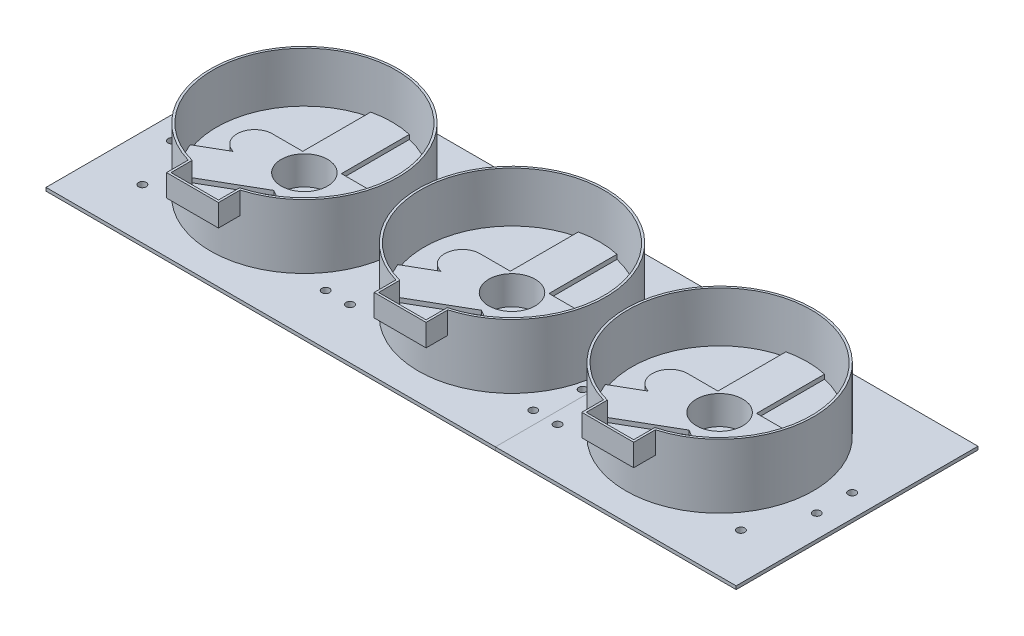
SolidWorks part; units mm, degrees
ref_plane "Front Plane" through (0, 0, 0) normal (0, 0, 1) x (1, 0, 0)
ref_plane "Top Plane" through (0, 0, 0) normal (0, 1, 0) x (1, 0, 0)
ref_plane "Right Plane" through (0, 0, 0) normal (1, 0, 0) x (0, 0, -1)
sketch "Sketch1" plane through (0, 0, 0) normal (0, 1, 0) x (1, 0, 0)
  line L1 (-151.5, 50) -> (151.5, 50)
  line L2 (-151.5, 50) -> (-151.5, -50)
  line L3 (-151.5, -50) -> (151.5, -50)
  line L4 (151.5, 50) -> (151.5, -50)
  line L5 (-151.5, 50) -> (151.5, -50) construction
  line L6 (-151.5, -50) -> (151.5, 50) construction
  point P0 (0, 0)
  dimension "D1" = 100
  dimension "D2" = 303
extrude "Boss-Extrude1" add sketch "Sketch1" along normal blind 3
sketch "Sketch2" plane through (0, 3, 0) normal (0, 1, 0) x (1, 0, 0)
  line L13 (-151.5, -50) -> (151.5, -50) construction
  line L14 (151.5, -50) -> (151.5, 50) construction
  line L15 (-151.5, 50) -> (-151.5, -50) construction
  line L16 (151.5, 50) -> (-151.5, 50) construction
  line L17 (-149.5, 48) -> (-149.5, -48)
  line L18 (-149.5, -48) -> (149.5, -48)
  line L19 (149.5, 48) -> (-149.5, 48)
  line L20 (149.5, -48) -> (149.5, 48)
  line L21 (-149.5, 48) -> (-149.5, -48)
  line L22 (-149.5, -48) -> (149.5, -48)
  line L23 (149.5, 48) -> (-149.5, 48)
  line L24 (149.5, -48) -> (149.5, 48)
  line L25 (-151.5, -50) -> (151.5, -50)
  line L26 (151.5, -50) -> (151.5, 50)
  line L27 (-151.5, 50) -> (-151.5, -50)
  line L28 (151.5, 50) -> (-151.5, 50)
  line M9 (151.5, -50) -> (151.5, 50)
  line M10 (151.5, 50) -> (-151.5, 50)
  line M11 (-151.5, 50) -> (-151.5, -50)
  line M12 (-151.5, -50) -> (151.5, -50)
  dimension "D1" = 2
extrude "Boss-Extrude3" add sketch "Sketch2" along normal blind 1.5 contours L24 L22 L21 L23 M12 M9 M10 M11
sketch "Sketch3" plane through (151.5, 0, 0) normal (1, 0, 0) x (0, 0, -1)
  line L0 (50, 4.5) -> (50, 0) construction
  line L1 (-50, 4.5) -> (50, 4.5)
  line L2 (-50, 4.5) -> (-50, 3)
  line L3 (-50, 3) -> (50, 3)
  line L4 (50, 4.5) -> (50, 3)
  dimension "D1" = 1.5
extrude "Boss-Extrude4" add sketch "Sketch3" along normal blind 4.75
sketch "Sketch5" plane through (0, 3, 0) normal (0, 1, 0) x (1, 0, 0)
  line L0 (149.5, -48) -> (149.5, 48) construction
  line L1 (0, 0) -> (0, 65.2785) construction
  line L2 (26.8157, -29.3425) -> (0, -13.8605)
  line L3 (-8.75, 38.775) -> (-8.75, 1.295)
  line L4 (8.75, 38.775) -> (8.75, 1.295)
  line L5 (36.8421, -14.924) -> (8.75, 1.295)
  line L6 (-36.8421, -14.924) -> (-8.75, 1.295)
  line L7 (-26.8157, -29.3425) -> (0, -13.8605)
  line L9 (-47, 60.0397) -> (-47, -70.5831) construction
  line L10 (5.6339, -7.0096) -> (33.9368, -23.3502) construction
  line L11 (-6.1109, -7.285) -> (-42.2034, -28.1229) construction
  line L12 (102.75, 38.775) -> (102.75, 1.295)
  line L13 (85.25, 38.775) -> (85.25, 1.295)
  line L14 (57.1579, -14.924) -> (85.25, 1.295)
  line L15 (67.1843, -29.3425) -> (94, -13.8605)
  line L16 (47, 76.7498) -> (47, -70.5831) construction
  line L17 (120.8157, -29.3425) -> (94, -13.8605)
  line L18 (130.8421, -14.924) -> (102.75, 1.295)
  line L19 (-67.1843, -29.3425) -> (-94, -13.8605)
  line L20 (-120.8157, -29.3425) -> (-94, -13.8605)
  line L21 (-130.8421, -14.924) -> (-102.75, 1.295)
  line L22 (-102.75, 38.775) -> (-102.75, 1.295)
  line L23 (-85.25, 38.775) -> (-85.25, 1.295)
  line L24 (-57.1579, -14.924) -> (-85.25, 1.295)
  circle A3 centre (0, 0) radius 39.75
  arc A6 (26.8157, -29.3425) -> (-26.8157, -29.3425) centre (0, 0) cw
  arc A7 (36.8421, -14.924) -> (8.75, 38.775) centre (0, 0) ccw
  arc A8 (-8.75, 38.775) -> (-36.8421, -14.924) centre (0, 0) ccw
  circle A9 centre (94, 0) radius 39.75
  circle A10 centre (-94, 0) radius 39.75
  dimension "D1" = 79.5
  dimension "D2" = 37.48
  dimension "D3" = 17.5
  dimension "D4" = 17.5
  dimension "D9" = 14.5
  dimension "D10" = 14.5
  dimension "D5" = 17.5
  dimension "D6" = 120
  dimension "D7" = 8.75
  dimension "D8" = 8.75
extrude "Cut-Extrude2" cut sketch "Sketch5" against normal blind 2 contours A10 L23 L24 | A10 L21 L22 | A10 L19 L20 | L3 A3 L6 | L7 A3 L2 | L5 A3 L4 | A9 L12 L18 | A9 L17 L15 | A9 L14 L13
sketch "Sketch6" plane through (0, 1, 0) normal (0, 1, 0) x (1, 0, 0)
  line L1 (-6.5, -26.3605) -> (6.5, -26.3605)
  line L2 (-8.5, -28.3605) -> (-8.5, -35.3605)
  line L3 (-6.5, -37.3605) -> (6.5, -37.3605)
  line L4 (8.5, -28.3605) -> (8.5, -35.3605)
  line L5 (-8.5, -26.3605) -> (8.5, -37.3605) construction
  line L6 (-8.5, -37.3605) -> (8.5, -26.3605) construction
  line L7 (-100.5, -26.3605) -> (-87.5, -26.3605)
  line L8 (-102.5, -28.3605) -> (-102.5, -35.3605)
  line L9 (-100.5, -37.3605) -> (-87.5, -37.3605)
  line L10 (-85.5, -28.3605) -> (-85.5, -35.3605)
  line L11 (-102.5, -26.3605) -> (-85.5, -37.3605) construction
  line L12 (-102.5, -37.3605) -> (-85.5, -26.3605) construction
  line L13 (87.5, -26.3605) -> (100.5, -26.3605)
  line L14 (85.5, -28.3605) -> (85.5, -35.3605)
  line L15 (87.5, -37.3605) -> (100.5, -37.3605)
  line L16 (102.5, -28.3605) -> (102.5, -35.3605)
  line L17 (85.5, -26.3605) -> (102.5, -37.3605) construction
  line L18 (85.5, -37.3605) -> (102.5, -26.3605) construction
  arc A0 (-6.5, -26.3605) -> (-8.5, -28.3605) centre (-6.5, -28.3605) ccw
  arc A1 (-8.5, -35.3605) -> (-6.5, -37.3605) centre (-6.5, -35.3605) ccw
  arc A2 (6.5, -37.3605) -> (8.5, -35.3605) centre (6.5, -35.3605) ccw
  arc A3 (6.5, -26.3605) -> (8.5, -28.3605) centre (6.5, -28.3605) cw
  arc A5 (-87.5, -37.3605) -> (-85.5, -35.3605) centre (-87.5, -35.3605) ccw
  arc A6 (-102.5, -35.3605) -> (-100.5, -37.3605) centre (-100.5, -35.3605) ccw
  arc A7 (-100.5, -26.3605) -> (-102.5, -28.3605) centre (-100.5, -28.3605) ccw
  arc A8 (-87.5, -26.3605) -> (-85.5, -28.3605) centre (-87.5, -28.3605) cw
  arc A9 (85.5, -35.3605) -> (87.5, -37.3605) centre (87.5, -35.3605) ccw
  arc A10 (100.5, -37.3605) -> (102.5, -35.3605) centre (100.5, -35.3605) ccw
  arc A11 (100.5, -26.3605) -> (102.5, -28.3605) centre (100.5, -28.3605) cw
  arc A12 (87.5, -26.3605) -> (85.5, -28.3605) centre (87.5, -28.3605) ccw
  point P0 (0, -31.8605)
  point P5 (-94, -31.8605)
  point P39 (94, -31.8605)
  dimension "D4" = 2
  dimension "D5" = 12.5
  dimension "D8" = 2
  dimension "D12" = 2
  dimension "D1" = 12.5
  dimension "D2" = 11
  dimension "D3" = 17
  dimension "D6" = 17
  dimension "D7" = 11
  dimension "D9" = 12.5
  dimension "D10" = 11
  dimension "D11" = 17
extrude "Cut-Extrude3" cut sketch "Sketch6" against normal through all both and the other way through all
mirror "Mirror1" about plane through (0, 0, 0) normal (1, 0, 0) of "Boss-Extrude4"
sketch "Sketch7" plane through (0, 0, 50) normal (0, 0, 1) x (1, 0, 0)
  line L1 (156.25, 4.5) -> (-156.25, 4.5)
  line L2 (156.25, 4.5) -> (156.25, 3)
  line L3 (156.25, 3) -> (-156.25, 3)
  line L4 (-156.25, 4.5) -> (-156.25, 3)
extrude "Boss-Extrude5" add sketch "Sketch7" along normal blind 4.75
mirror "Mirror2" about plane through (0, 0, 0) normal (0, 0, 1) of "Boss-Extrude5"
sketch "Sketch8" plane through (0, 3, 0) normal (0, 1, 0) x (1, 0, 0)
  line L0 (-22.5, 0) -> (22.5, 0) construction
  line L1 (-22.5, 8) -> (22.5, 8)
  line L2 (-22.5, -8) -> (22.5, -8)
  line L3 (47, 67.8149) -> (47, -81.6541) construction
  line L4 (-47, 71.8097) -> (-47, -81.6541) construction
  line L5 (116.5, 0) -> (71.5, 0) construction
  line L6 (116.5, 8) -> (71.5, 8)
  line L7 (116.5, -8) -> (71.5, -8)
  line L8 (-71.5, 0) -> (-116.5, 0) construction
  line L9 (-71.5, 8) -> (-116.5, 8)
  line L10 (-71.5, -8) -> (-116.5, -8)
  arc A0 (-22.5, 8) -> (-22.5, -8) centre (-22.5, 0) ccw
  arc A1 (22.5, -8) -> (22.5, 8) centre (22.5, 0) ccw
  arc A13 (116.5, 8) -> (116.5, -8) centre (116.5, 0) cw
  arc A14 (71.5, -8) -> (71.5, 8) centre (71.5, 0) cw
  arc A15 (-71.5, 8) -> (-71.5, -8) centre (-71.5, 0) cw
  arc A16 (-116.5, -8) -> (-116.5, 8) centre (-116.5, 0) cw
  point P2 (0, 0)
  point P15 (-94, 0)
  point P27 (94, 0)
  dimension "D2" = 8
  dimension "D1" = 45
  dimension "D3" = 94
  dimension "D4" = 47
extrude "Boss-Extrude6" add sketch "Sketch8" against normal up to surface (2 mm away) up to face at (-116.2558, 1, -10.5488)
sketch "Sketch9" plane through (0, 3, 0) normal (0, 1, 0) x (1, 0, 0)
  line L0 (-94, 61.6552) -> (-94, -65.6755) construction
  line L1 (94, 61.6552) -> (94, -59.8308) construction
  circle A0 centre (0, 0) radius 10.5
  circle A3 centre (94, 0) radius 10.5
  circle A4 centre (-94, 0) radius 10.5
  dimension "D1" = 21
  dimension "D2" = 21
  dimension "D3" = 21
  dimension "D4" = 94
  dimension "D5" = 94
extrude "Cut-Extrude4" cut sketch "Sketch9" against normal up to surface (2 mm away) up to face at (-118.1353, 1, -7.8892)
sketch "Sketch11" plane through (0, 1, 0) normal (0, 1, 0) x (1, 0, 0)
  circle A0 centre (0, 0) radius 6
  circle A1 centre (94, 0) radius 6
  circle A2 centre (-94, 0) radius 6
  circle A3 centre (94, 0) radius 10.5 construction
  dimension "D1" = 12
  dimension "D2" = 12
  dimension "D3" = 12
extrude "Cut-Extrude5" cut sketch "Sketch11" against normal through all both and the other way through all
sketch "Sketch12" plane through (0, 3, 0) normal (0, 1, 0) x (1, 0, 0)
  line L0 (116.5, 8) -> (102.75, 8) construction
  line L1 (130.8421, -14.924) -> (118.4371, -7.7619) construction
  line L2 (102.75, 38.775) -> (102.75, 8) construction
  line L3 (67.1843, -29.3425) -> (94, -13.8605) construction
  line L4 (120.8157, -29.3425) -> (94, -13.8605) construction
  line L5 (85.25, 38.775) -> (85.25, 8) construction
  line L6 (85.25, 8) -> (71.5, 8) construction
  line L7 (57.1579, -14.924) -> (69.5629, -7.7619) construction
  line L8 (36.8421, -14.924) -> (24.4371, -7.7619) construction
  line L9 (22.5, 8) -> (8.75, 8) construction
  line L10 (8.75, 38.775) -> (8.75, 8) construction
  line L11 (-26.8157, -29.3425) -> (0, -13.8605) construction
  line L12 (26.8157, -29.3425) -> (0, -13.8605) construction
  line L13 (-36.8421, -14.924) -> (-24.4371, -7.7619) construction
  line L14 (-8.75, 8) -> (-22.5, 8) construction
  line L15 (-8.75, 38.775) -> (-8.75, 8) construction
  line L16 (-57.1579, -14.924) -> (-69.5629, -7.7619) construction
  line L17 (-71.5, 8) -> (-85.25, 8) construction
  line L18 (-85.25, 38.775) -> (-85.25, 8) construction
  line L19 (-120.8157, -29.3425) -> (-94, -13.8605) construction
  line L20 (-67.1843, -29.3425) -> (-94, -13.8605) construction
  line L21 (-130.8421, -14.924) -> (-118.4371, -7.7619) construction
  line L22 (-102.75, 8) -> (-116.5, 8) construction
  line L23 (-102.75, 38.775) -> (-102.75, 8) construction
  line L24 (-149.5, 48) -> (-149.5, -48) construction
  line L25 (-149.5, -48) -> (149.5, -48) construction
  line L26 (149.5, -48) -> (149.5, 48) construction
  line L27 (149.5, 48) -> (-149.5, 48) construction
  line L28 (116.5, 8) -> (102.75, 8)
  line L29 (130.8421, -14.924) -> (118.4371, -7.7619)
  line L30 (102.75, 38.775) -> (102.75, 8)
  line L31 (67.1843, -29.3425) -> (94, -13.8605)
  line L32 (120.8157, -29.3425) -> (94, -13.8605)
  line L33 (85.25, 38.775) -> (85.25, 8)
  line L34 (85.25, 8) -> (71.5, 8)
  line L35 (57.1579, -14.924) -> (69.5629, -7.7619)
  line L36 (36.8421, -14.924) -> (24.4371, -7.7619)
  line L37 (22.5, 8) -> (8.75, 8)
  line L38 (8.75, 38.775) -> (8.75, 8)
  line L39 (-26.8157, -29.3425) -> (0, -13.8605)
  line L40 (26.8157, -29.3425) -> (0, -13.8605)
  line L41 (-36.8421, -14.924) -> (-24.4371, -7.7619)
  line L42 (-8.75, 8) -> (-22.5, 8)
  line L43 (-8.75, 38.775) -> (-8.75, 8)
  line L44 (-57.1579, -14.924) -> (-69.5629, -7.7619)
  line L45 (-71.5, 8) -> (-85.25, 8)
  line L46 (-85.25, 38.775) -> (-85.25, 8)
  line L47 (-120.8157, -29.3425) -> (-94, -13.8605)
  line L48 (-67.1843, -29.3425) -> (-94, -13.8605)
  line L49 (-130.8421, -14.924) -> (-118.4371, -7.7619)
  line L50 (-102.75, 8) -> (-116.5, 8)
  line L51 (-102.75, 38.775) -> (-102.75, 8)
  line L52 (-149.5, 48) -> (-149.5, -48)
  line L53 (-149.5, -48) -> (149.5, -48)
  line L54 (149.5, -48) -> (149.5, 48)
  line L55 (149.5, 48) -> (-149.5, 48)
  arc A0 (118.4371, -7.7619) -> (116.5, 8) centre (116.5, 0) ccw construction
  arc A1 (130.8421, -14.924) -> (102.75, 38.775) centre (94, 0) ccw construction
  arc A2 (67.1843, -29.3425) -> (120.8157, -29.3425) centre (94, 0) ccw construction
  circle A3 centre (94, 0) radius 10.5 construction
  arc A4 (71.5, 8) -> (69.5629, -7.7619) centre (71.5, 0) ccw construction
  arc A5 (85.25, 38.775) -> (57.1579, -14.924) centre (94, 0) ccw construction
  arc A6 (24.4371, -7.7619) -> (22.5, 8) centre (22.5, 0) ccw construction
  arc A7 (36.8421, -14.924) -> (8.75, 38.775) centre (0, 0) ccw construction
  arc A8 (-26.8157, -29.3425) -> (26.8157, -29.3425) centre (0, 0) ccw construction
  circle A9 centre (0, 0) radius 10.5 construction
  arc A10 (-22.5, 8) -> (-24.4371, -7.7619) centre (-22.5, 0) ccw construction
  arc A11 (-8.75, 38.775) -> (-36.8421, -14.924) centre (0, 0) ccw construction
  circle A12 centre (-94, 0) radius 10.5 construction
  arc A13 (-69.5629, -7.7619) -> (-71.5, 8) centre (-71.5, 0) ccw construction
  arc A14 (-57.1579, -14.924) -> (-85.25, 38.775) centre (-94, 0) ccw construction
  arc A15 (-120.8157, -29.3425) -> (-67.1843, -29.3425) centre (-94, 0) ccw construction
  arc A16 (-116.5, 8) -> (-118.4371, -7.7619) centre (-116.5, 0) ccw construction
  arc A17 (-102.75, 38.775) -> (-130.8421, -14.924) centre (-94, 0) ccw construction
  arc A18 (118.4371, -7.7619) -> (116.5, 8) centre (116.5, 0) ccw
  arc A19 (130.8421, -14.924) -> (102.75, 38.775) centre (94, 0) ccw
  arc A20 (67.1843, -29.3425) -> (120.8157, -29.3425) centre (94, 0) ccw
  circle A21 centre (94, 0) radius 10.5
  arc A22 (71.5, 8) -> (69.5629, -7.7619) centre (71.5, 0) ccw
  arc A23 (85.25, 38.775) -> (57.1579, -14.924) centre (94, 0) ccw
  arc A24 (24.4371, -7.7619) -> (22.5, 8) centre (22.5, 0) ccw
  arc A25 (36.8421, -14.924) -> (8.75, 38.775) centre (0, 0) ccw
  arc A26 (-26.8157, -29.3425) -> (26.8157, -29.3425) centre (0, 0) ccw
  circle A27 centre (0, 0) radius 10.5
  arc A28 (-22.5, 8) -> (-24.4371, -7.7619) centre (-22.5, 0) ccw
  arc A29 (-8.75, 38.775) -> (-36.8421, -14.924) centre (0, 0) ccw
  circle A30 centre (-94, 0) radius 10.5
  arc A31 (-69.5629, -7.7619) -> (-71.5, 8) centre (-71.5, 0) ccw
  arc A32 (-57.1579, -14.924) -> (-85.25, 38.775) centre (-94, 0) ccw
  arc A33 (-120.8157, -29.3425) -> (-67.1843, -29.3425) centre (-94, 0) ccw
  arc A34 (-116.5, 8) -> (-118.4371, -7.7619) centre (-116.5, 0) ccw
  arc A35 (-102.75, 38.775) -> (-130.8421, -14.924) centre (-94, 0) ccw
extrude "Boss-Extrude8" add sketch "Sketch12" along normal blind 11
sketch "Sketch13" plane through (0, 1, 0) normal (0, 1, 0) x (1, 0, 0)
  line L0 (87.5, -37.3605) -> (100.5, -37.3605) construction
  line L1 (102.5, -35.3605) -> (102.5, -28.3605) construction
  line L2 (85.5, -28.3605) -> (85.5, -35.3605) construction
  line L3 (100.5, -26.3605) -> (87.5, -26.3605) construction
  line L4 (-85.5, -35.3605) -> (-85.5, -28.3605) construction
  line L5 (-100.5, -37.3605) -> (-87.5, -37.3605) construction
  line L6 (-102.5, -28.3605) -> (-102.5, -35.3605) construction
  line L7 (-87.5, -26.3605) -> (-100.5, -26.3605) construction
  line L8 (-6.5, -37.3605) -> (6.5, -37.3605) construction
  line L9 (8.5, -35.3605) -> (8.5, -28.3605) construction
  line L10 (6.5, -26.3605) -> (-6.5, -26.3605) construction
  line L11 (-8.5, -28.3605) -> (-8.5, -35.3605) construction
  line L12 (87.5, -37.3605) -> (100.5, -37.3605)
  line L13 (102.5, -35.3605) -> (102.5, -28.3605)
  line L14 (85.5, -28.3605) -> (85.5, -35.3605)
  line L15 (100.5, -26.3605) -> (87.5, -26.3605)
  line L16 (-85.5, -35.3605) -> (-85.5, -28.3605)
  line L17 (-100.5, -37.3605) -> (-87.5, -37.3605)
  line L18 (-102.5, -28.3605) -> (-102.5, -35.3605)
  line L19 (-87.5, -26.3605) -> (-100.5, -26.3605)
  line L20 (-6.5, -37.3605) -> (6.5, -37.3605)
  line L21 (8.5, -35.3605) -> (8.5, -28.3605)
  line L22 (6.5, -26.3605) -> (-6.5, -26.3605)
  line L23 (-8.5, -28.3605) -> (-8.5, -35.3605)
  line L24 (120.8157, -29.3425) -> (94, -13.8605) construction
  line L25 (67.1843, -29.3425) -> (94, -13.8605) construction
  line L26 (26.8157, -29.3425) -> (0, -13.8605) construction
  line L27 (-26.8157, -29.3425) -> (0, -13.8605) construction
  line L28 (-120.8157, -29.3425) -> (-94, -13.8605) construction
  line L29 (-67.1843, -29.3425) -> (-94, -13.8605) construction
  line L30 (120.8157, -29.3425) -> (94, -13.8605)
  line L31 (67.1843, -29.3425) -> (94, -13.8605)
  line L32 (26.8157, -29.3425) -> (0, -13.8605)
  line L33 (-26.8157, -29.3425) -> (0, -13.8605)
  line L34 (-120.8157, -29.3425) -> (-94, -13.8605)
  line L35 (-67.1843, -29.3425) -> (-94, -13.8605)
  line L36 (118.4371, -7.7619) -> (130.8421, -14.924) construction
  line L37 (102.75, 38.775) -> (102.75, 8) construction
  line L38 (102.75, 8) -> (116.5, 8) construction
  line L39 (71.5, 8) -> (85.25, 8) construction
  line L40 (85.25, 8) -> (85.25, 38.775) construction
  line L41 (57.1579, -14.924) -> (69.5629, -7.7619) construction
  line L42 (8.75, 8) -> (22.5, 8) construction
  line L43 (24.4371, -7.7619) -> (36.8421, -14.924) construction
  line L44 (8.75, 38.775) -> (8.75, 8) construction
  line L45 (-22.5, 8) -> (-8.75, 8) construction
  line L46 (-8.75, 8) -> (-8.75, 38.775) construction
  line L47 (-36.8421, -14.924) -> (-24.4371, -7.7619) construction
  line L48 (-116.5, 8) -> (-102.75, 8) construction
  line L49 (-102.75, 8) -> (-102.75, 38.775) construction
  line L50 (-130.8421, -14.924) -> (-118.4371, -7.7619) construction
  line L51 (-69.5629, -7.7619) -> (-57.1579, -14.924) construction
  line L52 (-85.25, 38.775) -> (-85.25, 8) construction
  line L53 (-85.25, 8) -> (-71.5, 8) construction
  line L54 (118.4371, -7.7619) -> (130.8421, -14.924)
  line L55 (102.75, 38.775) -> (102.75, 8)
  line L56 (102.75, 8) -> (116.5, 8)
  line L57 (71.5, 8) -> (85.25, 8)
  line L58 (85.25, 8) -> (85.25, 38.775)
  line L59 (57.1579, -14.924) -> (69.5629, -7.7619)
  line L60 (8.75, 8) -> (22.5, 8)
  line L61 (24.4371, -7.7619) -> (36.8421, -14.924)
  line L62 (8.75, 38.775) -> (8.75, 8)
  line L63 (-22.5, 8) -> (-8.75, 8)
  line L64 (-8.75, 8) -> (-8.75, 38.775)
  line L65 (-36.8421, -14.924) -> (-24.4371, -7.7619)
  line L66 (-116.5, 8) -> (-102.75, 8)
  line L67 (-102.75, 8) -> (-102.75, 38.775)
  line L68 (-130.8421, -14.924) -> (-118.4371, -7.7619)
  line L69 (-69.5629, -7.7619) -> (-57.1579, -14.924)
  line L70 (-85.25, 38.775) -> (-85.25, 8)
  line L71 (-85.25, 8) -> (-71.5, 8)
  arc A0 (85.5, -35.3605) -> (87.5, -37.3605) centre (87.5, -35.3605) ccw construction
  arc A1 (100.5, -37.3605) -> (102.5, -35.3605) centre (100.5, -35.3605) ccw construction
  arc A2 (87.5, -26.3605) -> (85.5, -28.3605) centre (87.5, -28.3605) ccw construction
  arc A3 (102.5, -28.3605) -> (100.5, -26.3605) centre (100.5, -28.3605) ccw construction
  arc A4 (-85.5, -28.3605) -> (-87.5, -26.3605) centre (-87.5, -28.3605) ccw construction
  arc A5 (-87.5, -37.3605) -> (-85.5, -35.3605) centre (-87.5, -35.3605) ccw construction
  arc A6 (-102.5, -35.3605) -> (-100.5, -37.3605) centre (-100.5, -35.3605) ccw construction
  arc A7 (-100.5, -26.3605) -> (-102.5, -28.3605) centre (-100.5, -28.3605) ccw construction
  arc A8 (-8.5, -35.3605) -> (-6.5, -37.3605) centre (-6.5, -35.3605) ccw construction
  arc A9 (6.5, -37.3605) -> (8.5, -35.3605) centre (6.5, -35.3605) ccw construction
  arc A10 (8.5, -28.3605) -> (6.5, -26.3605) centre (6.5, -28.3605) ccw construction
  arc A11 (-6.5, -26.3605) -> (-8.5, -28.3605) centre (-6.5, -28.3605) ccw construction
  arc A12 (85.5, -35.3605) -> (87.5, -37.3605) centre (87.5, -35.3605) ccw
  arc A13 (100.5, -37.3605) -> (102.5, -35.3605) centre (100.5, -35.3605) ccw
  arc A14 (87.5, -26.3605) -> (85.5, -28.3605) centre (87.5, -28.3605) ccw
  arc A15 (102.5, -28.3605) -> (100.5, -26.3605) centre (100.5, -28.3605) ccw
  arc A16 (-85.5, -28.3605) -> (-87.5, -26.3605) centre (-87.5, -28.3605) ccw
  arc A17 (-87.5, -37.3605) -> (-85.5, -35.3605) centre (-87.5, -35.3605) ccw
  arc A18 (-102.5, -35.3605) -> (-100.5, -37.3605) centre (-100.5, -35.3605) ccw
  arc A19 (-100.5, -26.3605) -> (-102.5, -28.3605) centre (-100.5, -28.3605) ccw
  arc A20 (-8.5, -35.3605) -> (-6.5, -37.3605) centre (-6.5, -35.3605) ccw
  arc A21 (6.5, -37.3605) -> (8.5, -35.3605) centre (6.5, -35.3605) ccw
  arc A22 (8.5, -28.3605) -> (6.5, -26.3605) centre (6.5, -28.3605) ccw
  arc A23 (-6.5, -26.3605) -> (-8.5, -28.3605) centre (-6.5, -28.3605) ccw
  arc A24 (67.1843, -29.3425) -> (120.8157, -29.3425) centre (94, 0) ccw construction
  arc A25 (-26.8157, -29.3425) -> (26.8157, -29.3425) centre (0, 0) ccw construction
  arc A26 (-120.8157, -29.3425) -> (-67.1843, -29.3425) centre (-94, 0) ccw construction
  arc A27 (67.1843, -29.3425) -> (120.8157, -29.3425) centre (94, 0) ccw
  arc A28 (-26.8157, -29.3425) -> (26.8157, -29.3425) centre (0, 0) ccw
  arc A29 (-120.8157, -29.3425) -> (-67.1843, -29.3425) centre (-94, 0) ccw
  arc A30 (118.4371, -7.7619) -> (116.5, 8) centre (116.5, 0) ccw construction
  arc A31 (130.8421, -14.924) -> (102.75, 38.775) centre (94, 0) ccw construction
  arc A32 (71.5, 8) -> (69.5629, -7.7619) centre (71.5, 0) ccw construction
  arc A33 (85.25, 38.775) -> (57.1579, -14.924) centre (94, 0) ccw construction
  arc A34 (24.4371, -7.7619) -> (22.5, 8) centre (22.5, 0) ccw construction
  arc A35 (36.8421, -14.924) -> (8.75, 38.775) centre (0, 0) ccw construction
  arc A36 (-22.5, 8) -> (-24.4371, -7.7619) centre (-22.5, 0) ccw construction
  arc A37 (-8.75, 38.775) -> (-36.8421, -14.924) centre (0, 0) ccw construction
  arc A38 (-116.5, 8) -> (-118.4371, -7.7619) centre (-116.5, 0) ccw construction
  arc A39 (-102.75, 38.775) -> (-130.8421, -14.924) centre (-94, 0) ccw construction
  arc A40 (-69.5629, -7.7619) -> (-71.5, 8) centre (-71.5, 0) ccw construction
  arc A41 (-57.1579, -14.924) -> (-85.25, 38.775) centre (-94, 0) ccw construction
  arc A42 (118.4371, -7.7619) -> (116.5, 8) centre (116.5, 0) ccw
  arc A43 (130.8421, -14.924) -> (102.75, 38.775) centre (94, 0) ccw
  arc A44 (71.5, 8) -> (69.5629, -7.7619) centre (71.5, 0) ccw
  arc A45 (85.25, 38.775) -> (57.1579, -14.924) centre (94, 0) ccw
  arc A46 (24.4371, -7.7619) -> (22.5, 8) centre (22.5, 0) ccw
  arc A47 (36.8421, -14.924) -> (8.75, 38.775) centre (0, 0) ccw
  arc A48 (-22.5, 8) -> (-24.4371, -7.7619) centre (-22.5, 0) ccw
  arc A49 (-8.75, 38.775) -> (-36.8421, -14.924) centre (0, 0) ccw
  arc A50 (-116.5, 8) -> (-118.4371, -7.7619) centre (-116.5, 0) ccw
  arc A51 (-102.75, 38.775) -> (-130.8421, -14.924) centre (-94, 0) ccw
  arc A52 (-69.5629, -7.7619) -> (-71.5, 8) centre (-71.5, 0) ccw
  arc A53 (-57.1579, -14.924) -> (-85.25, 38.775) centre (-94, 0) ccw
extrude "Boss-Extrude10" add sketch "Sketch13" along normal blind 11
sketch "Sketch14" plane through (0, 0, 0) normal (0, -1, 0) x (-1, 0, 0)
  line L0 (8.5, -28.3605) -> (8.5, -35.3605) construction
  line L1 (-85.5, -28.3605) -> (-85.5, -35.3605) construction
  line L2 (83, -26.3605) -> (77, -26.3605)
  line L3 (83, -26.3605) -> (83, -37.3605)
  line L4 (83, -37.3605) -> (77, -37.3605)
  line L5 (77, -26.3605) -> (77, -37.3605)
  line L6 (85.5, -35.3605) -> (85.5, -28.3605) construction
  line L7 (102.5, -28.3605) -> (102.5, -35.3605) construction
  line L8 (110, -37.3605) -> (104, -37.3605)
  line L9 (110, -37.3605) -> (110, -26.3605)
  line L10 (110, -26.3605) -> (104, -26.3605)
  line L11 (104, -37.3605) -> (104, -26.3605)
  line L12 (110, -37.3605) -> (104, -26.3605) construction
  line L13 (110, -26.3605) -> (104, -37.3605) construction
  line L14 (47, -76.9208) -> (47, 109.7683) construction
  line L15 (-47, -76.9208) -> (-47, 82.5761) construction
  line L16 (-17, -26.3605) -> (-11, -26.3605)
  line L17 (-11, -37.3605) -> (-11, -26.3605)
  line L18 (-17, -37.3605) -> (-11, -37.3605)
  line L19 (-17, -37.3605) -> (-17, -26.3605)
  line L20 (10, -37.3605) -> (16, -37.3605)
  line L21 (16, -26.3605) -> (16, -37.3605)
  line L22 (10, -26.3605) -> (16, -26.3605)
  line L23 (10, -26.3605) -> (10, -37.3605)
  line L24 (-105, -26.3605) -> (-105, -37.3605)
  line L25 (-105, -26.3605) -> (-111, -26.3605)
  line L26 (-111, -26.3605) -> (-111, -37.3605)
  line L27 (-105, -37.3605) -> (-111, -37.3605)
  line L28 (-78, -37.3605) -> (-78, -26.3605)
  line L29 (-78, -37.3605) -> (-84, -37.3605)
  line L30 (-84, -37.3605) -> (-84, -26.3605)
  line L31 (-78, -26.3605) -> (-84, -26.3605)
  line L32 (-8.5, -35.3605) -> (-8.5, -28.3605) construction
  line L33 (176.0137, -14.43) -> (-236.6755, -14.43) construction
  line L58 (-102.5, -35.3605) -> (-102.5, -28.3605) construction
  point P6 (85.5, -31.8605)
  point P7 (83, -31.8605)
  point P8 (107, -31.8605)
  point P16 (102.5, -31.8605)
  point P67 (-11, -31.8605)
  dimension "D1" = 11
  dimension "D2" = 6
  dimension "D3" = 2.5
  dimension "D4" = 1.5
  dimension "D5" = 6
  dimension "D6" = 11
  dimension "D7" = 47
  dimension "D8" = 47
  dimension "D9" = 14.43
  dimension "D10" = 1.5
  dimension "D11" = 2.5
  dimension "D12" = 11
  dimension "D13" = 6
  dimension "D14" = 1.5
  dimension "D15" = 6
  dimension "D16" = 11
  dimension "D17" = 2.5
  dimension "D18" = 6
  dimension "D19" = 11
sketch "Sketch16" plane through (0, 0, 0) normal (0, -1, 0) x (1, 0, 0)
  line L0 (-94, 37.3605) -> (-94, -37.0305) construction
  line L1 (21.5, 5.5) -> (27.5, 5.5)
  line L2 (21.5, 5.5) -> (21.5, -5.5)
  line L3 (21.5, -5.5) -> (27.5, -5.5)
  line L4 (27.5, 5.5) -> (27.5, -5.5)
  line L5 (21.5, 5.5) -> (27.5, -5.5) construction
  line L6 (21.5, -5.5) -> (27.5, 5.5) construction
  line L7 (-27.5, 5.5) -> (-21.5, 5.5)
  line L8 (-27.5, 5.5) -> (-27.5, -5.5)
  line L9 (-27.5, -5.5) -> (-21.5, -5.5)
  line L10 (-21.5, 5.5) -> (-21.5, -5.5)
  line L11 (-27.5, 5.5) -> (-21.5, -5.5) construction
  line L12 (-27.5, -5.5) -> (-21.5, 5.5) construction
  line L13 (-72.5, 5.5) -> (-66.5, 5.5)
  line L14 (-72.5, 5.5) -> (-72.5, -5.5)
  line L15 (-72.5, -5.5) -> (-66.5, -5.5)
  line L16 (-66.5, 5.5) -> (-66.5, -5.5)
  line L17 (-72.5, 5.5) -> (-66.5, -5.5) construction
  line L18 (-72.5, -5.5) -> (-66.5, 5.5) construction
  line L19 (-121.5, 5.5) -> (-115.5, 5.5)
  line L20 (-121.5, 5.5) -> (-121.5, -5.5)
  line L21 (-121.5, -5.5) -> (-115.5, -5.5)
  line L22 (-115.5, 5.5) -> (-115.5, -5.5)
  line L23 (-121.5, 5.5) -> (-115.5, -5.5) construction
  line L24 (-121.5, -5.5) -> (-115.5, 5.5) construction
  line L25 (-100.5, 37.3605) -> (-87.5, 37.3605) construction
  line L26 (94, 26.3605) -> (94, -31.2539) construction
  line L27 (100.5, 26.3605) -> (87.5, 26.3605) construction
  line L29 (115.5, 5.5) -> (121.5, 5.5)
  line L30 (115.5, 5.5) -> (115.5, -5.5)
  line L31 (115.5, -5.5) -> (121.5, -5.5)
  line L32 (121.5, 5.5) -> (121.5, -5.5)
  line L33 (115.5, 5.5) -> (121.5, -5.5) construction
  line L34 (115.5, -5.5) -> (121.5, 5.5) construction
  line L35 (66.5, 5.5) -> (72.5, 5.5)
  line L36 (66.5, 5.5) -> (66.5, -5.5)
  line L37 (66.5, -5.5) -> (72.5, -5.5)
  line L38 (72.5, 5.5) -> (72.5, -5.5)
  line L39 (66.5, 5.5) -> (72.5, -5.5) construction
  line L40 (66.5, -5.5) -> (72.5, 5.5) construction
  point P0 (24.5, 0)
  point P5 (-24.5, 0)
  point P10 (-69.5, 0)
  point P16 (-118.5, 0)
  point P29 (118.5, 0)
  point P34 (69.5, 0)
  dimension "D1" = 49
  dimension "D2" = 24.5
  dimension "D3" = 6
  dimension "D4" = 11
  dimension "D5" = 6
  dimension "D6" = 11
  dimension "D7" = 6
  dimension "D8" = 11
  dimension "D9" = 49
  dimension "D10" = 24.5
  dimension "D11" = 49
  dimension "D12" = 24.5
sketch "Sketch18" plane through (0, 14, 0) normal (0, 1, 0) x (1, 0, 0)
  line L9 (149.5, -48) -> (149.5, 48) construction
  line L10 (149.5, 48) -> (-149.5, 48) construction
  line L11 (-149.5, 48) -> (-149.5, -48) construction
  line L12 (-149.5, -48) -> (149.5, -48) construction
  line L13 (149.5, -48) -> (149.5, 48)
  line L14 (149.5, 48) -> (-149.5, 48)
  line L15 (-149.5, 48) -> (-149.5, -48)
  line L16 (-149.5, -48) -> (149.5, -48)
  arc A0 (-8.75, 38.775) -> (8.75, 38.775) centre (0, 0) cw
  arc A1 (36.8421, -14.924) -> (26.8157, -29.3425) centre (0, 0) cw
  arc A3 (-26.8157, -29.3425) -> (-36.8421, -14.924) centre (0, 0) cw
  arc A4 (-102.75, 38.775) -> (-85.25, 38.775) centre (-94, 0) cw
  arc A5 (-57.1579, -14.924) -> (-67.1843, -29.3425) centre (-94, 0) cw
  arc A6 (-120.8157, -29.3425) -> (-130.8421, -14.924) centre (-94, 0) cw
  arc A7 (130.8421, -14.924) -> (120.8157, -29.3425) centre (94, 0) cw
  arc A8 (67.1843, -29.3425) -> (57.1579, -14.924) centre (94, 0) cw
  arc A9 (85.25, 38.775) -> (102.75, 38.775) centre (94, 0) cw
  arc A10 (-120.8157, -29.3425) -> (-67.1843, -29.3425) centre (-94, 0) ccw construction
  arc A11 (-57.1579, -14.924) -> (-85.25, 38.775) centre (-94, 0) ccw construction
  arc A12 (-102.75, 38.775) -> (-130.8421, -14.924) centre (-94, 0) ccw construction
  arc A13 (-26.8157, -29.3425) -> (26.8157, -29.3425) centre (0, 0) ccw construction
  arc A14 (-8.75, 38.775) -> (-36.8421, -14.924) centre (0, 0) ccw construction
  arc A15 (36.8421, -14.924) -> (8.75, 38.775) centre (0, 0) ccw construction
  arc A16 (67.1843, -29.3425) -> (120.8157, -29.3425) centre (94, 0) ccw construction
  arc A17 (85.25, 38.775) -> (57.1579, -14.924) centre (94, 0) ccw construction
  arc A18 (130.8421, -14.924) -> (102.75, 38.775) centre (94, 0) ccw construction
  arc A19 (-120.8157, -29.3425) -> (-67.1843, -29.3425) centre (-94, 0) ccw
  arc A20 (-57.1579, -14.924) -> (-85.25, 38.775) centre (-94, 0) ccw
  arc A21 (-102.75, 38.775) -> (-130.8421, -14.924) centre (-94, 0) ccw
  arc A22 (-26.8157, -29.3425) -> (26.8157, -29.3425) centre (0, 0) ccw
  arc A23 (-8.75, 38.775) -> (-36.8421, -14.924) centre (0, 0) ccw
  arc A24 (36.8421, -14.924) -> (8.75, 38.775) centre (0, 0) ccw
  arc A25 (67.1843, -29.3425) -> (120.8157, -29.3425) centre (94, 0) ccw
  arc A26 (85.25, 38.775) -> (57.1579, -14.924) centre (94, 0) ccw
  arc A27 (130.8421, -14.924) -> (102.75, 38.775) centre (94, 0) ccw
extrude "Cut-Extrude8" cut sketch "Sketch18" against normal up to surface (9.5 mm away) up to face at (0, 4.5, 0)
sketch "Sketch20" plane through (0, 4.5, 0) normal (0, 1, 0) x (1, 0, 0)
  circle A0 centre (94, 0) radius 42.5
  circle A1 centre (0, 0) radius 42.5
  circle A2 centre (-94, 0) radius 42.5
  dimension "D1" = 85
extrude "Extrude-Thin1" add sketch "Sketch20" along normal blind 19 thin contours A0 thin type one direction reverse wall 1
ref_plane "Plane1" through (47.25, 0, 0) normal (1, 0, 0) x (0, 0, -1)
sketch "Sketch21" plane through (0, 0, 0) normal (0, -1, 0) x (1, 0, 0)
  line L0 (-102.5, 28.3605) -> (-102.5, 35.3605) construction
  line L1 (0, -12.925) -> (0, 12.925) construction
  line L2 (47.25, 61.1487) -> (47.25, -66.5425) construction
  line L3 (156.25, 54.75) -> (156.25, -54.75) construction
  line L9 (102.5, 35.3605) -> (102.5, 28.3605) construction
  line L10 (85.5, 28.3605) -> (85.5, 35.3605) construction
  line L11 (8.5, 35.3605) -> (8.5, 28.3605) construction
  line L12 (-8.5, 28.3605) -> (-8.5, 35.3605) construction
  line L13 (-85.5, 35.3605) -> (-85.5, 28.3605) construction
  circle A0 centre (41.5, 31.8605) radius 1.75
  circle A1 centre (-41.5, 31.8605) radius 1.75
  circle A2 centre (135.5, 31.8605) radius 1.75
  circle A3 centre (52.5, 31.8605) radius 1.75
  circle A4 centre (-135.5, 31.8605) radius 1.75
  circle A5 centre (-52.5, 31.8605) radius 1.75
  circle A6 centre (-146, -8) radius 1.75
  circle A11 centre (146, -8) radius 1.75
  circle A13 centre (94, 0) radius 6 construction
  circle A15 centre (-94, 0) radius 6 construction
  circle A16 centre (146, 8) radius 1.75
  circle A17 centre (-146, 8) radius 1.75
  circle A18 centre (44.5, -12.5) radius 1.75
  circle A19 centre (44.5, 12.5) radius 1.75
  point P14 (-102.5, 31.8605)
  dimension "D1" = 3.5
  dimension "D3" = 33
  dimension "D5" = 33
  dimension "D6" = 33
  dimension "D7" = 33
  dimension "D2" = 33
  dimension "D4" = 33
  dimension "D8" = 8
  dimension "D9" = 8
  dimension "D10" = 46
  dimension "D11" = 46
  dimension "D12" = 16
  dimension "D13" = 109
  dimension "D14" = 1
  dimension "D15" = 25
  dimension "D16" = 12.5
extrude "Cut-Extrude9" cut sketch "Sketch21" against normal through all both
sketch "Sketch23" plane through (0, 23.5, 0) normal (0, 1, 0) x (1, 0, 0)
  line L0 (-83.25, -41.118) -> (-83.25, -49.658)
  line L1 (-104.75, -41.118) -> (-104.75, -49.658)
  line L2 (-104.75, -49.658) -> (-83.25, -49.658)
  line L3 (-105.75, -41.118) -> (-105.75, -50.658)
  line L4 (-105.75, -50.658) -> (-82.25, -50.658)
  line L5 (-82.25, -41.118) -> (-82.25, -50.658)
  line L6 (-105.75, -41.118) -> (-105.75, -40.8435)
  line L7 (-82.25, -40.8435) -> (-82.25, -41.118)
  line L8 (-104.75, -41.118) -> (-104.75, -40.0835)
  line L9 (-83.25, -41.118) -> (-83.25, -40.0835)
  circle A2 centre (-94, 0) radius 41.5 construction
  circle A3 centre (-94, 0) radius 42.5
  arc A4 (-83.25, -41.118) -> (-104.75, -41.118) centre (-94, 0) ccw
  circle A5 centre (-94, 0) radius 41.5
  circle M5 centre (-94, 0) radius 42.5
  circle M6 centre (-94, 0) radius 41.5
  dimension "D1" = 0
  dimension "D2" = 21.5
  dimension "D3" = 8.54
  dimension "D4" = 1
extrude "Boss-Extrude13" add sketch "Sketch23" along normal blind 10 contours L9 L8 M5 M6 | L7 L0 L2 L1 L6 L3 L4 L5 M5
pattern_linear "LPattern1" count 3 spacing 94 along (1, 0, 0) of "Boss-Extrude13"
sketch "Sketch22" plane through (0, 4.5, 0) normal (0, 1, 0) x (1, 0, 0)
  line L0 (47.25, 78.0013) -> (47.25, -110.844) construction
  line L1 (156.25, 54.75) -> (156.25, -54.75) construction
  dimension "D1" = 109
ref_plane "Plane2" through (47.25, 0, 0) normal (1, 0, 0) x (0, 0, -1)
split "Split1" trim tools "Plane2" bodies to split 135 resulting bodies 136 137
